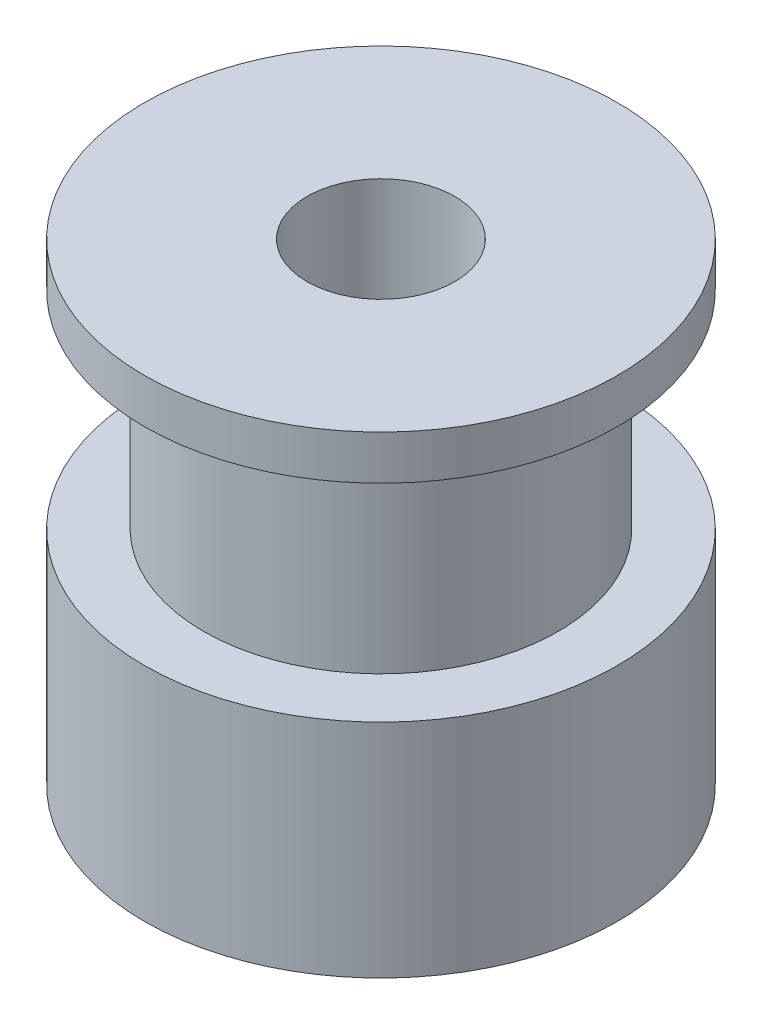
SolidWorks part; units mm, degrees
material "Liga 1060"
ref_plane "Plano frontal" through (0, 0, 0) normal (0, 0, 1) x (1, 0, 0)
ref_plane "Plano superior" through (0, 0, 0) normal (0, 1, 0) x (1, 0, 0)
ref_plane "Plano direito" through (0, 0, 0) normal (1, 0, 0) x (0, 0, -1)
sketch "Esboço1" plane through (0, 0, 0) normal (0, 0, 1) x (1, 0, 0)
  line L0 (0, 15.0124) -> (0, -4.167) construction
  line L1 (2.5, 16) -> (8, 16)
  line L2 (8, 16) -> (8, 14.5)
  line L3 (8, 14.5) -> (6, 14.5)
  line L4 (6, 14.5) -> (6, 7.5)
  line L5 (6, 7.5) -> (8, 7.5)
  line L6 (8, 7.5) -> (8, 0)
  line L7 (8, 0) -> (2.5, 0)
  line L8 (2.5, 16) -> (2.5, 0)
  point P3 (5.25, 0)
  dimension "D1" = 5
  dimension "D2" = 16
  dimension "D3" = 16
  dimension "D4" = 7.5
  dimension "D5" = 7
  dimension "D6" = 12
revolve "Revolução1" add sketch "Esboço1" angle 360 about L0
